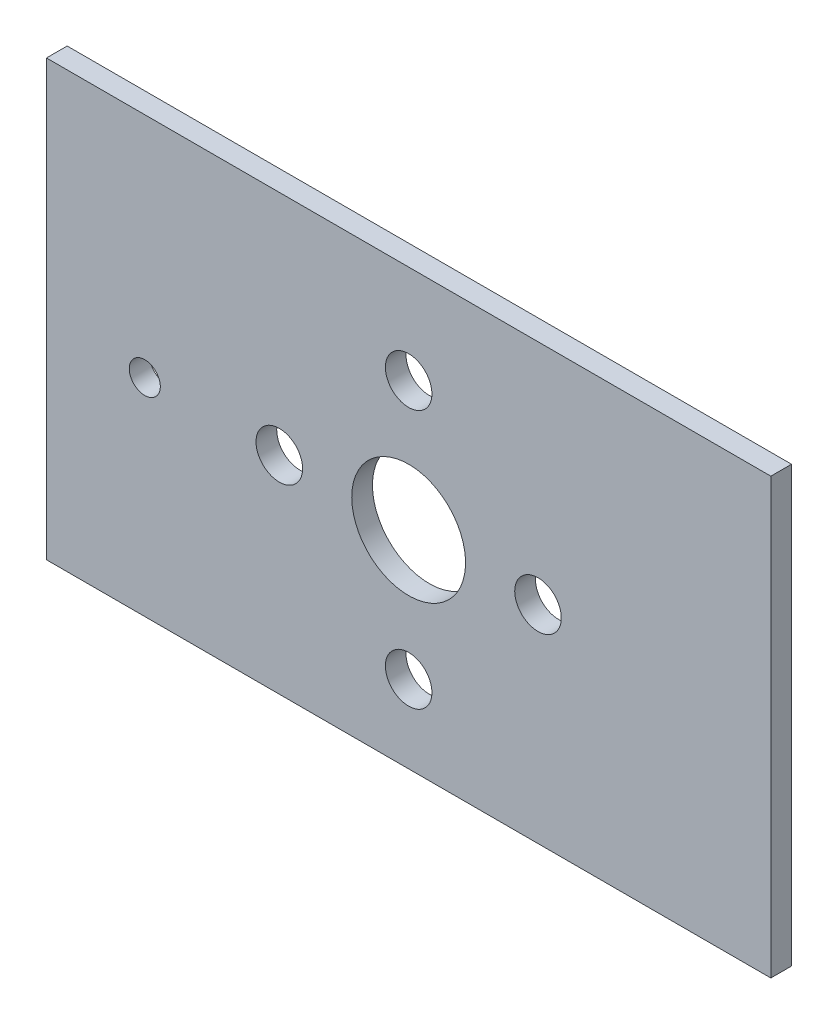
SolidWorks part; units mm, degrees
ref_plane "Plan de face" through (0, 0, 0) normal (0, 0, 1) x (1, 0, 0)
ref_plane "Plan de dessus" through (0, 0, 0) normal (0, 1, 0) x (1, 0, 0)
ref_plane "Plan de droite" through (0, 0, 0) normal (1, 0, 0) x (0, 0, -1)
sketch "Esquisse1" plane through (0, 0, 0) normal (0, 0, 1) x (1, 0, 0)
  line L1 (0, 0) -> (70, 0)
  line L2 (0, 0) -> (0, 42)
  line L3 (0, 42) -> (70, 42)
  line L4 (70, 0) -> (70, 42)
  dimension "D1" = 70
  dimension "D2" = 42
extrude "Boss.-Extru.1" add sketch "Esquisse1" along normal blind 2
sketch "Esquisse2" plane through (0, 0, 0) normal (0, 0, -1) x (-1, 0, 0)
  line L0 (-35, 42) -> (-35, 0) construction
  line L1 (-70, 42) -> (0, 42) construction
  line L2 (0, 0) -> (-70, 0) construction
  line L3 (-35, 20) -> (-70, 20) construction
  line L4 (-70, 0) -> (-70, 42) construction
  line L5 (-70, 20) -> (0, 20) construction
  line L6 (0, 42) -> (0, 0) construction
  circle A0 centre (-9.5, 20) radius 1.5
  point P6 (-35, 32.5)
  point P7 (-35, 7.5)
  point P8 (-35, 20)
  point P13 (-47.5, 20)
  point P17 (-22.5, 20)
  point P18 (-9.5, 20)
  dimension "D1" = 9.5
  dimension "D2" = 25
  dimension "D3" = 12.5
  dimension "D4" = 12.5
  dimension "D5" = 12.5
  dimension "D6" = 25.5
hole_wizard "Dégagement M41" positions "Esquisse3D1" profile "Esquisse3" hole size "M4" standard "ISO" end condition through all
sketch3d "Esquisse3D1"
  point P0 (35, 32.5, 0)
  point P3 (47.5, 20, 0)
  point P6 (35, 7.5, 0)
  point P9 (22.5, 20, 0)
sketch "Esquisse3" plane through (35, 32.5, 0) normal (1, 0, 0) x (0, 1, 0)
  line L0 (0, 0) -> (0, 2)
  line L1 (0, 2) -> (2.25, 2)
  line L2 (2.25, 2) -> (2.25, 0)
  line L5 (2.25, 0) -> (0, 0)
  line L11 (0, -6.35) -> (0, 107.95) construction
  dimension "Diamètre du perçage jusqu'au prochain" = 4.5
  dimension "Profondeur du perçage jusqu'au prochain" = 2
sketch "Esquisse4" plane through (0, 0, 0) normal (0, 0, -1) x (-1, 0, 0)
  circle A0 centre (-35, 20) radius 5.5
  dimension "D1" = 11
extrude "Enlèv. mat.-Extru.1" cut sketch "Esquisse4" against normal through all
extrude "Enlèv. mat.-Extru.2" cut sketch "Esquisse2" against normal through all contours A0
